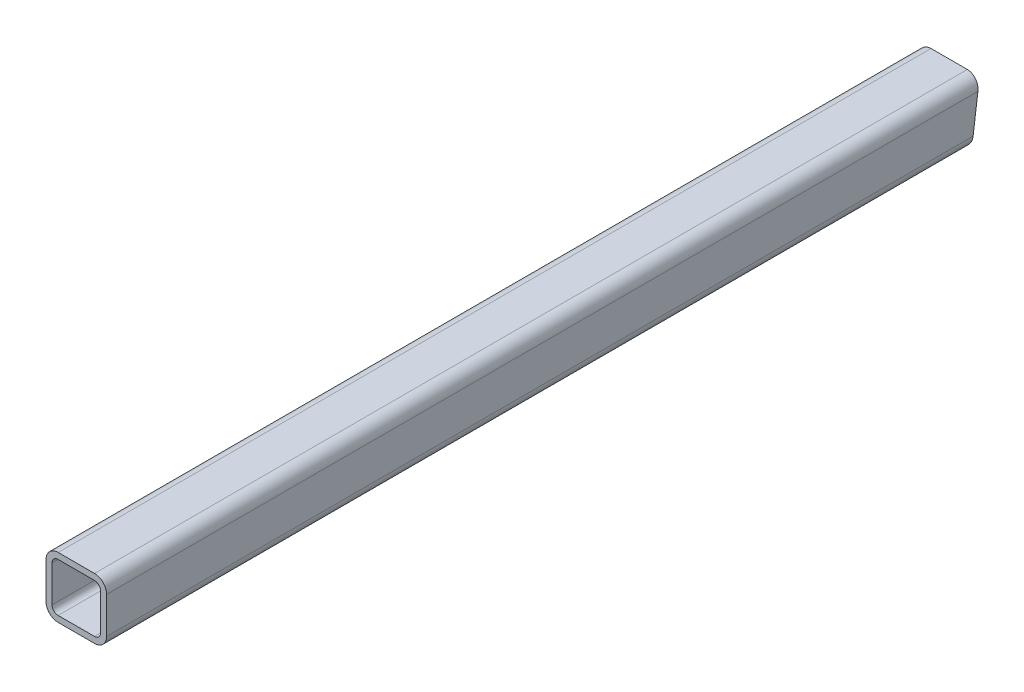
SolidWorks part; units mm, degrees
ref_plane "Front Plane" through (0, 0, 0) normal (0, 0, 1) x (1, 0, 0)
ref_plane "Top Plane" through (0, 0, 0) normal (0, 1, 0) x (1, 0, 0)
ref_plane "Right Plane" through (0, 0, 0) normal (1, 0, 0) x (0, 0, -1)
sketch "Sketch1" plane through (0, 0, 0) normal (0, 0, 1) x (1, 0, 0)
  line L0 (-19.05, -25.4) -> (19.05, -25.4)
  line L1 (-25.4, -19.05) -> (-25.4, 19.05)
  line L2 (19.05, 25.4) -> (-19.05, 25.4)
  line L3 (25.4, 19.05) -> (25.4, -19.05)
  line L4 (-19.05, -31.75) -> (19.05, -31.75)
  line L5 (-31.75, -19.05) -> (-31.75, 19.05)
  line L6 (19.05, 31.75) -> (-19.05, 31.75)
  line L7 (31.75, 19.05) -> (31.75, -19.05)
  line L10 (-25.4, 0) -> (25.4, 0)
  arc A0 (31.75, 19.05) -> (19.05, 31.75) centre (19.05, 19.05) ccw
  arc A1 (19.05, -31.75) -> (31.75, -19.05) centre (19.05, -19.05) ccw
  arc A2 (-31.75, -19.05) -> (-19.05, -31.75) centre (-19.05, -19.05) ccw
  arc A3 (-19.05, 31.75) -> (-31.75, 19.05) centre (-19.05, 19.05) ccw
  arc A4 (-19.05, 25.4) -> (-25.4, 19.05) centre (-19.05, 19.05) ccw
  arc A5 (25.4, 19.05) -> (19.05, 25.4) centre (19.05, 19.05) ccw
  arc A6 (19.05, -25.4) -> (25.4, -19.05) centre (19.05, -19.05) ccw
  arc A7 (-25.4, -19.05) -> (-19.05, -25.4) centre (-19.05, -19.05) ccw
  dimension "D1" = 12.7
  dimension "D2" = 6.35
  dimension "D3" = 6.35
  dimension "D4" = 50.8
  dimension "D5" = 50.8
  dimension "D6" = 6.35
  dimension "D7" = 63.5
  dimension "D8" = 63.5
extrude "Boss-Extrude1" add sketch "Sketch1" along normal mid plane 914.4 contours L6 A3 L5 A2 L4 A1 L7 A0 A7 L1 A4 L2 A5 L3 A6 L0
sketch "Sketch2" plane through (31.75, 0, 0) normal (1, 0, 0) x (0, 0, -1)
  line L0 (-457.2, 31.75) -> (457.2, 31.75) construction
  line L1 (-457.2, 31.75) -> (457.2, 31.75)
  line L2 (457.2, 31.75) -> (457.2, -68.1782)
  line L3 (457.2, -68.1782) -> (444.0442, -68.1782)
  line L4 (444.0442, -68.1782) -> (457.2, 31.75)
  line M1 (457.2, -19.05) -> (457.2, 19.05)
  line M2 (457.2, 19.05) -> (-457.2, 19.05)
  line M4 (-457.2, -19.05) -> (457.2, -19.05)
  dimension "D1" = 7.5
extrude "Cut-Extrude1" cut sketch "Sketch2" against normal blind 914.4 contours L4 L3 L2 M4 | L4 M4 M1 M2
